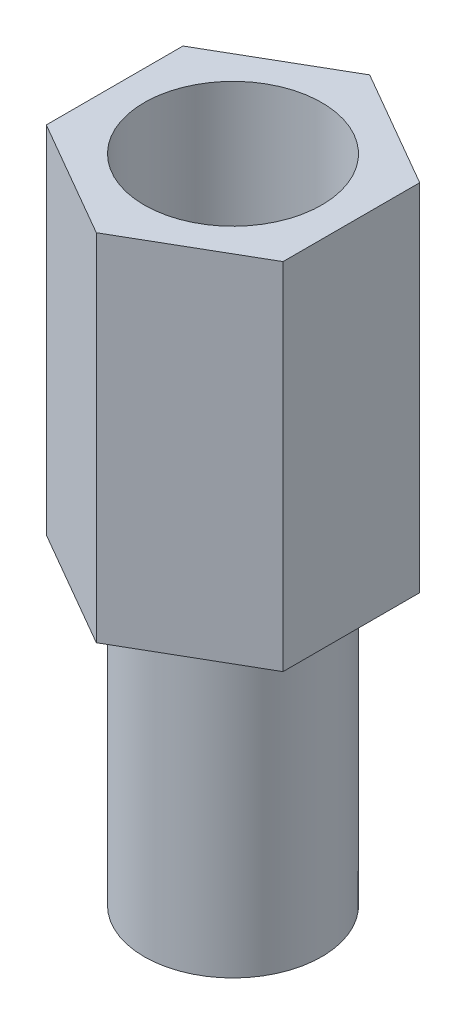
SolidWorks part; units mm, degrees
ref_plane "前视基准面" through (0, 0, 0) normal (0, 0, 1) x (1, 0, 0)
ref_plane "上视基准面" through (0, 0, 0) normal (0, 1, 0) x (1, 0, 0)
ref_plane "右视基准面" through (0, 0, 0) normal (1, 0, 0) x (0, 0, -1)
sketch "草图1" plane through (0, 0, 0) normal (0, 1, 0) x (1, 0, 0)
  circle A0 centre (0, 0) radius 1.5
extrude "凸台-拉伸1" add sketch "草图1" along normal blind 5
sketch "草图2" plane through (0, 5, 0) normal (0, 1, 0) x (1, 0, 0)
  line L1 (0, 2.3094) -> (-2, 1.1547)
  line L2 (-2, 1.1547) -> (-2, -1.1547)
  line L3 (-2, -1.1547) -> (0, -2.3094)
  line L4 (0, -2.3094) -> (2, -1.1547)
  line L5 (2, -1.1547) -> (2, 1.1547)
  line L6 (2, 1.1547) -> (0, 2.3094)
  circle A0 centre (0, 0) radius 2 construction
extrude "凸台-拉伸2" add sketch "草图2" along normal blind 6
sketch "草图3" plane through (0, 11, 0) normal (0, 1, 0) x (1, 0, 0)
  circle A0 centre (0, 0) radius 1.5
extrude "切除-拉伸1" cut sketch "草图3" against normal blind 5
